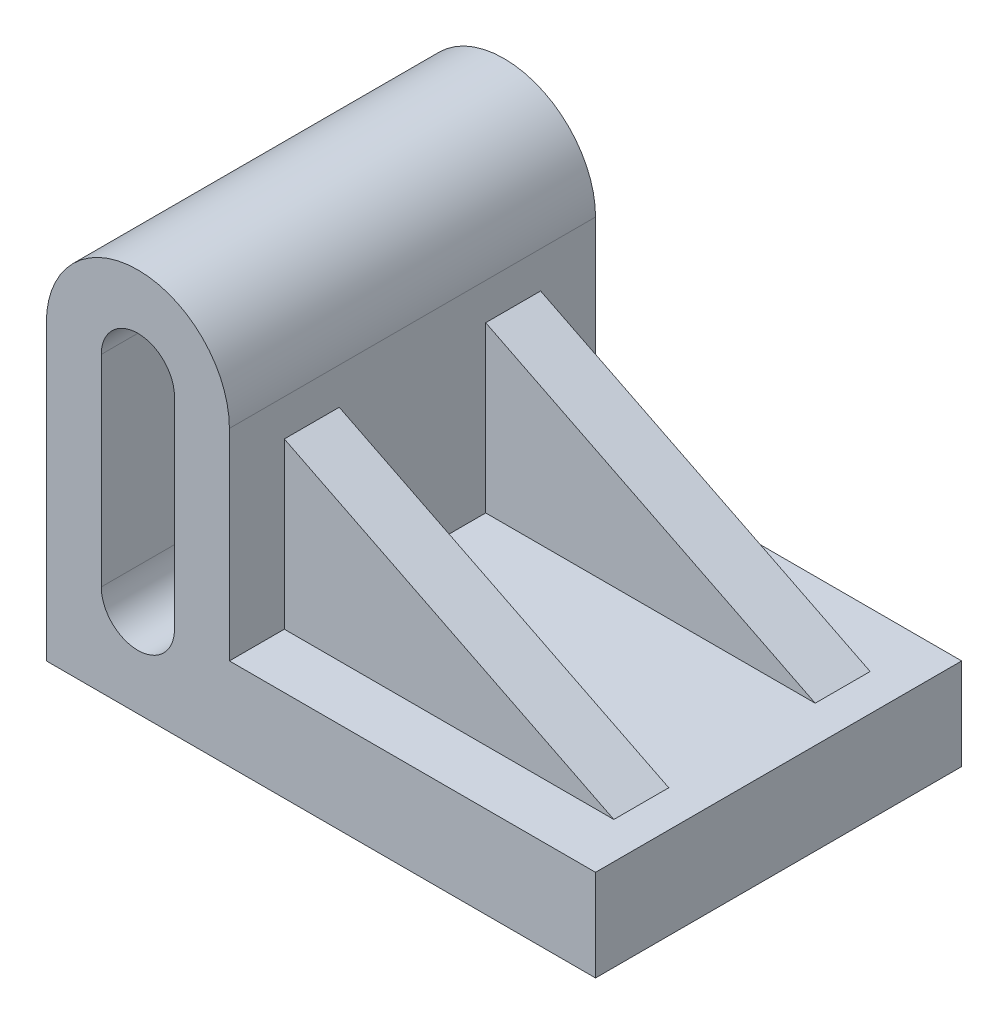
SolidWorks part; units mm, degrees
ref_plane "Front Plane" through (0, 0, 0) normal (0, 0, 1) x (1, 0, 0)
ref_plane "Top Plane" through (0, 0, 0) normal (0, 1, 0) x (1, 0, 0)
ref_plane "Right Plane" through (0, 0, 0) normal (1, 0, 0) x (0, 0, -1)
sketch "Sketch1" plane through (0, 0, 0) normal (0, 0, 1) x (1, 0, 0)
  line L0 (-77.1171, 57.8153) -> (-77.1171, 2.8153) construction
  line L1 (-52.1171, 57.8153) -> (-52.1171, 2.8153)
  line L2 (-102.1171, 57.8153) -> (-102.1171, 2.8153)
  line L3 (-77.1171, 57.8153) -> (-77.1171, 2.8153) construction
  line L4 (-67.1171, 57.8153) -> (-67.1171, 2.8153)
  line L5 (-87.1171, 57.8153) -> (-87.1171, 2.8153)
  line L6 (-102.1171, 2.8153) -> (-102.1171, -22.1847)
  line L7 (-102.1171, -22.1847) -> (47.8829, -22.1847)
  line L8 (47.8829, -22.1847) -> (47.8829, 2.8153)
  line L9 (47.8829, 2.8153) -> (-52.1171, 2.8153)
  arc A0 (-52.1171, 57.8153) -> (-102.1171, 57.8153) centre (-77.1171, 57.8153) ccw
  arc A2 (-67.1171, 57.8153) -> (-87.1171, 57.8153) centre (-77.1171, 57.8153) ccw
  arc A3 (-87.1171, 2.8153) -> (-67.1171, 2.8153) centre (-77.1171, 2.8153) ccw
  point P2 (-77.1171, 30.3153)
  point P9 (-77.1171, 30.3153)
  dimension "D1" = 25
  dimension "D2" = 10
  dimension "D3" = 55
  dimension "D4" = 25
  dimension "D5" = 150
  dimension "D6" = 25
extrude "Boss-Extrude1" add sketch "Sketch1" against normal blind 100
sketch "Sketch4" plane through (0, 2.8153, 0) normal (0, 1, 0) x (1, 0, 0)
  line L0 (-52.1171, 100) -> (-52.1171, 0) construction
  line L1 (37.8829, 15) -> (-52.1171, 15)
  line L2 (37.8829, 15) -> (37.8829, 85)
  line L3 (37.8829, 85) -> (-52.1171, 85)
  line L4 (-52.1171, 15) -> (-52.1171, 85)
  line L5 (47.8829, 0) -> (-52.1171, 0) construction
  line L6 (47.8829, 100) -> (-52.1171, 100) construction
  line L7 (47.8829, 100) -> (47.8829, 0) construction
  dimension "D1" = 15
  dimension "D2" = 15
  dimension "D3" = 10
extrude "Boss-Extrude2" add sketch "Sketch4" along normal blind 45
sketch "Sketch5" plane through (37.8829, 0, 0) normal (1, 0, 0) x (0, 0, -1)
  line L0 (15, 47.8153) -> (85, 47.8153) construction
  line L1 (30, 47.8153) -> (70, 47.8153)
  line L2 (30, 47.8153) -> (30, 2.8153)
  line L3 (30, 2.8153) -> (70, 2.8153)
  line L4 (70, 47.8153) -> (70, 2.8153)
  line L5 (15, 2.8153) -> (85, 2.8153) construction
  line L6 (15, 47.8153) -> (15, 2.8153) construction
  dimension "D1" = 40
  dimension "D2" = 15
extrude "Cut-Extrude1" cut sketch "Sketch5" against normal blind 90
sketch "Sketch6" plane through (0, 0, -15) normal (0, 0, 1) x (1, 0, 0)
  line L0 (-52.1171, 47.8153) -> (37.8829, 2.8153)
  line L1 (37.8829, 2.8153) -> (37.8829, 47.8153)
  line L2 (37.8829, 47.8153) -> (-52.1171, 47.8153)
extrude "Cut-Extrude2" cut sketch "Sketch6" against normal blind 70
